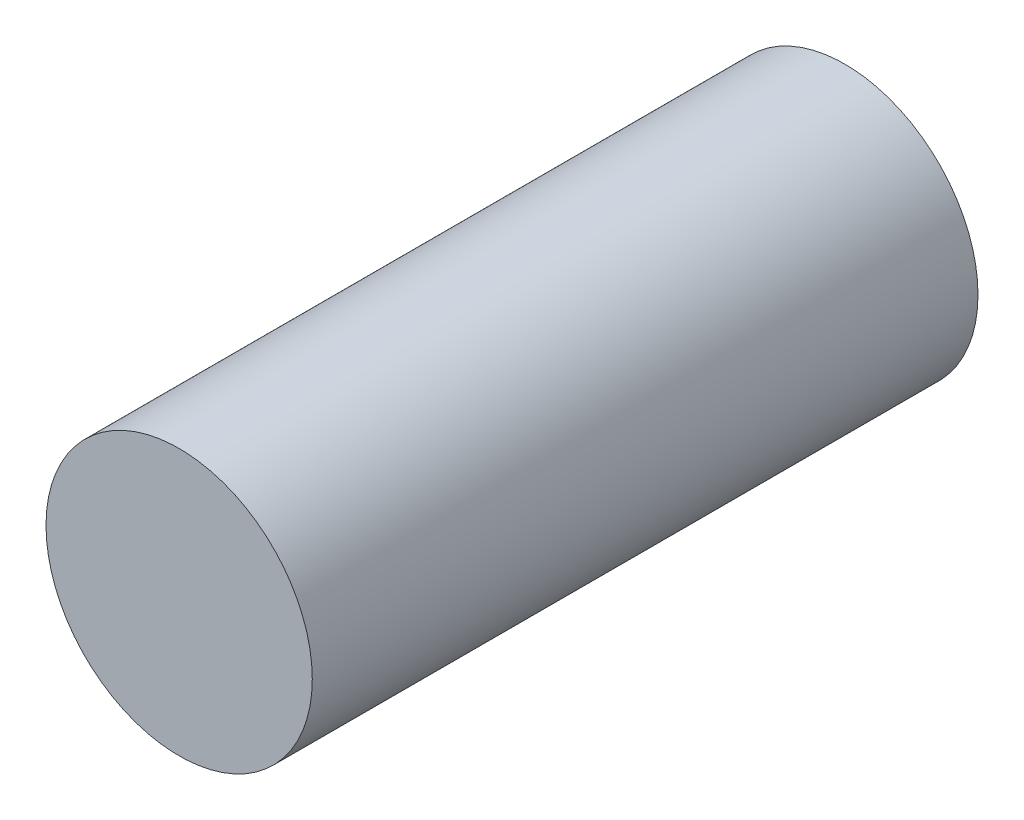
SolidWorks part; units mm, degrees
ref_plane "Front Plane" through (0, 0, 0) normal (0, 0, 1) x (1, 0, 0)
ref_plane "Top Plane" through (0, 0, 0) normal (0, 1, 0) x (1, 0, 0)
ref_plane "Right Plane" through (0, 0, 0) normal (1, 0, 0) x (0, 0, -1)
sketch "Sketch1" plane through (0, 0, 0) normal (0, 0, 1) x (1, 0, 0)
  circle A0 centre (0, 0) radius 12
  dimension "D1" = 24
extrude "Boss-Extrude1" add sketch "Sketch1" along normal blind 60
